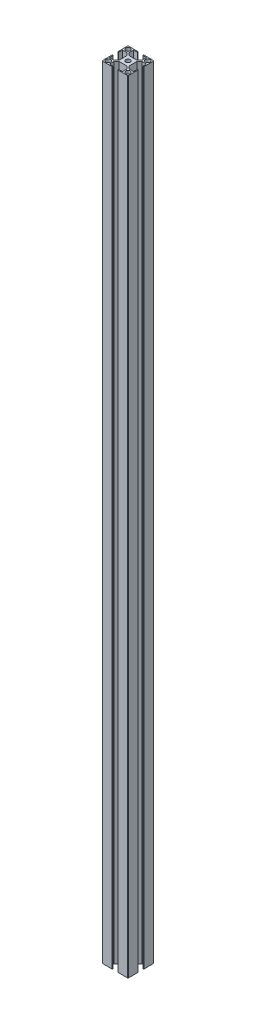
SolidWorks part; units mm, degrees
ref_plane "Front Plane" through (0, 0, 0) normal (0, 0, 1) x (1, 0, 0)
ref_plane "Top Plane" through (0, 0, 0) normal (0, 1, 0) x (1, 0, 0)
ref_plane "Right Plane" through (0, 0, 0) normal (1, 0, 0) x (0, 0, -1)
sketch "Sketch1" plane through (0, 0, 0) normal (0, 1, 0) x (1, 0, 0)
  line L0 (20, 19) -> (20, -19)
  line L1 (-19, -20) -> (19, -20)
  line L2 (-20, -19) -> (-20, 19)
  line L3 (-19, 20) -> (19, 20)
  line L5 (-20, -20) -> (20, 0) construction
  line L6 (-20, 20) -> (20, 0) construction
  line L7 (-20, 20) -> (20, -20) construction
  line L8 (20, 20) -> (-20, -20) construction
  line L9 (-20, 0) -> (20, 0) construction
  line L10 (-10, -18.5) -> (10, -18.5)
  line L11 (10, -18.5) -> (10, -11.825)
  line L12 (10, -11.825) -> (5.875, -7.7)
  line L13 (5.875, -7.7) -> (-5.875, -7.7)
  line L14 (-5.875, -7.7) -> (-10, -11.825)
  line L15 (-10, -11.825) -> (-10, -18.5)
  line L16 (-11.825, -10) -> (-18.5, -10)
  line L17 (-7.7, -5.875) -> (-11.825, -10)
  line L18 (-7.7, 5.875) -> (-7.7, -5.875)
  line L19 (-11.825, 10) -> (-7.7, 5.875)
  line L20 (-18.5, 10) -> (-11.825, 10)
  line L21 (-18.5, -10) -> (-18.5, 10)
  line L22 (-10, 11.825) -> (-10, 18.5)
  line L23 (-5.875, 7.7) -> (-10, 11.825)
  line L24 (5.875, 7.7) -> (-5.875, 7.7)
  line L25 (10, 11.825) -> (5.875, 7.7)
  line L26 (10, 18.5) -> (10, 11.825)
  line L27 (-10, 18.5) -> (10, 18.5)
  line L28 (0, 20) -> (0, -20) construction
  line L29 (18.5, -10) -> (18.5, 10)
  line L30 (18.5, 10) -> (11.825, 10)
  line L31 (11.825, 10) -> (7.7, 5.875)
  line L32 (7.7, 5.875) -> (7.7, -5.875)
  line L33 (7.7, -5.875) -> (11.825, -10)
  line L34 (11.825, -10) -> (18.5, -10)
  line L35 (15.1625, -10) -> (15.1625, -15.1625) construction
  arc A0 (-19, -20) -> (-20, -19) centre (-19, -19) cw
  arc A1 (20, -19) -> (19, -20) centre (19, -19) cw
  arc A2 (20, 19) -> (19, 20) centre (19, 19) ccw
  arc A3 (-19, 20) -> (-20, 19) centre (-19, 19) ccw
  circle A4 centre (15.1625, -15.1625) radius 3.5
  circle A5 centre (-15.1625, -15.1625) radius 3.5
  circle A6 centre (-15.1625, 15.1625) radius 3.5
  circle A7 centre (15.1625, 15.1625) radius 3.5
  circle A8 centre (0, 0) radius 3.5
  point P30 (0, 0)
  point P31 (0, 18.5)
  point P59 (0, 0)
  dimension "D7" = 1
  dimension "D8" = 7
  dimension "D10" = 7
  dimension "D1" = 40
  dimension "D2" = 40
  dimension "D3" = 10.8
  dimension "D4" = 11.75
  dimension "D5" = 20
  dimension "D6" = 1.5
  dimension "D9" = 4
extrude "Boss-Extrude1" add sketch "Sketch1" along normal blind 1200
sketch "Sketch2" plane through (0, 1200, 0) normal (0, 1, 0) x (1, 0, 0)
  line L0 (-4.65, 20) -> (-4.65, 19.35)
  line L1 (19, 20) -> (-19, 20) construction
  line L2 (-4.55, 19.25) -> (-4.25, 19.25)
  line L3 (-4.15, 19.15) -> (-4.15, 18.5)
  line L4 (10, 18.5) -> (-10, 18.5) construction
  line L5 (0, 20) -> (0, 18.5) construction
  line L6 (4.15, 19.15) -> (4.15, 18.5)
  line L7 (4.55, 19.25) -> (4.25, 19.25)
  line L8 (4.65, 20) -> (4.65, 19.35)
  line L9 (-4.65, 20) -> (4.65, 20)
  line L10 (-4.15, 18.5) -> (4.15, 18.5)
  line L11 (20, 4.65) -> (19.35, 4.65)
  line L12 (19.25, 4.55) -> (19.25, 4.25)
  line L13 (19.15, 4.15) -> (18.5, 4.15)
  line L14 (19.15, -4.15) -> (18.5, -4.15)
  line L15 (19.25, -4.55) -> (19.25, -4.25)
  line L16 (20, -4.65) -> (19.35, -4.65)
  line L17 (20, 4.65) -> (20, -4.65)
  line L18 (18.5, 4.15) -> (18.5, -4.15)
  line L19 (20, 0) -> (18.5, 0) construction
  line L20 (4.65, -20) -> (4.65, -19.35)
  line L21 (4.55, -19.25) -> (4.25, -19.25)
  line L22 (4.15, -19.15) -> (4.15, -18.5)
  line L23 (-4.15, -19.15) -> (-4.15, -18.5)
  line L24 (-4.55, -19.25) -> (-4.25, -19.25)
  line L25 (-4.65, -20) -> (-4.65, -19.35)
  line L26 (4.65, -20) -> (-4.65, -20)
  line L27 (4.15, -18.5) -> (-4.15, -18.5)
  line L28 (0, -20) -> (0, -18.5) construction
  line L29 (-20, -4.65) -> (-19.35, -4.65)
  line L30 (-19.25, -4.55) -> (-19.25, -4.25)
  line L31 (-19.15, -4.15) -> (-18.5, -4.15)
  line L32 (-19.15, 4.15) -> (-18.5, 4.15)
  line L33 (-19.25, 4.55) -> (-19.25, 4.25)
  line L34 (-20, 4.65) -> (-19.35, 4.65)
  line L35 (-20, -4.65) -> (-20, 4.65)
  line L36 (-18.5, -4.15) -> (-18.5, 4.15)
  line L37 (-20, 0) -> (-18.5, 0) construction
  arc A0 (4.55, 19.25) -> (4.65, 19.35) centre (4.55, 19.35) ccw
  arc A1 (4.25, 19.25) -> (4.15, 19.15) centre (4.25, 19.15) ccw
  arc A2 (-4.15, 19.15) -> (-4.25, 19.25) centre (-4.25, 19.15) ccw
  arc A3 (-4.65, 19.35) -> (-4.55, 19.25) centre (-4.55, 19.35) ccw
  arc A4 (19.25, -4.55) -> (19.35, -4.65) centre (19.35, -4.55) ccw
  arc A5 (19.25, -4.25) -> (19.15, -4.15) centre (19.15, -4.25) ccw
  arc A6 (19.15, 4.15) -> (19.25, 4.25) centre (19.15, 4.25) ccw
  arc A7 (19.35, 4.65) -> (19.25, 4.55) centre (19.35, 4.55) ccw
  arc A8 (-4.55, -19.25) -> (-4.65, -19.35) centre (-4.55, -19.35) ccw
  arc A9 (-4.25, -19.25) -> (-4.15, -19.15) centre (-4.25, -19.15) ccw
  arc A10 (4.15, -19.15) -> (4.25, -19.25) centre (4.25, -19.15) ccw
  arc A11 (4.65, -19.35) -> (4.55, -19.25) centre (4.55, -19.35) ccw
  arc A12 (-19.25, 4.55) -> (-19.35, 4.65) centre (-19.35, 4.55) ccw
  arc A13 (-19.25, 4.25) -> (-19.15, 4.15) centre (-19.15, 4.25) ccw
  arc A14 (-19.15, -4.15) -> (-19.25, -4.25) centre (-19.15, -4.25) ccw
  arc A15 (-19.35, -4.65) -> (-19.25, -4.55) centre (-19.35, -4.55) ccw
  point P16 (4.65, 19.25)
  point P19 (4.15, 19.25)
  point P22 (-4.15, 19.25)
  point P25 (-4.65, 19.25)
  point P83 (0, 0)
  dimension "D4" = 0.1
  dimension "D1" = 0.75
  dimension "D2" = 0.5
  dimension "D3" = 4.15
  dimension "D5" = 4
extrude "Cut-Extrude1" cut sketch "Sketch2" against normal through all
